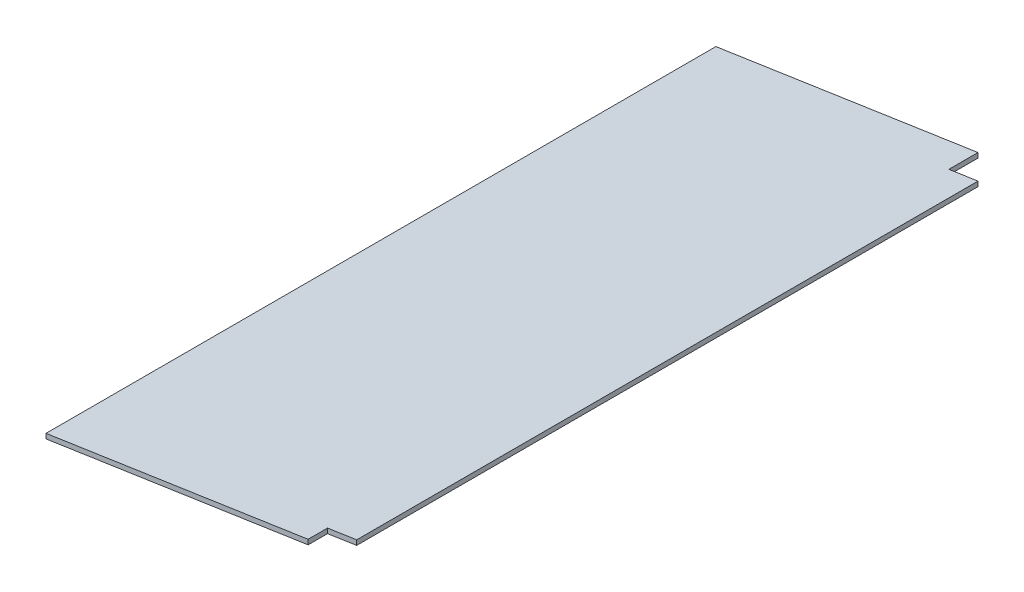
SolidWorks part; units mm, degrees
ref_plane "Front Plane" through (0, 0, 0) normal (0, 0, 1) x (1, 0, 0)
ref_plane "Top Plane" through (0, 0, 0) normal (0, 1, 0) x (1, 0, 0)
ref_plane "Right Plane" through (0, 0, 0) normal (1, 0, 0) x (0, 0, -1)
sketch "Sketch1" plane through (0, 0, 0) normal (0, 0, 1) x (1, 0, 0)
  line L0 (0, 0) -> (0, 5)
  line L1 (0, 0) -> (300, 0)
  line L2 (300, 0) -> (300, 50)
  line L3 (300, 50) -> (0, 5)
  line L4 (0, 0) -> (300, 45)
  dimension "D1" = 5
  dimension "D2" = 5
  dimension "D3" = 300
  dimension "D4" = 50
extrude "Boss-Extrude1" add sketch "Sketch1" along normal blind 690 contours L0 L4 L2 L3
sketch "Sketch3" plane through (0, 0, 0) normal (0, 1, 0) x (1, 0, 0)
  line L0 (270, -690) -> (300, -690)
  line L1 (300, -690) -> (300, -670)
  line L2 (300, -30) -> (300, 0)
  line L3 (300, -690) -> (270, -690)
  line L4 (300, -690) -> (300, -670)
  line L5 (300, -670) -> (270, -670)
  line L6 (270, -690) -> (270, -670)
  line L7 (300, 0) -> (270, 0)
  line L8 (300, 0) -> (300, -30)
  line L9 (300, -30) -> (270, -30)
  line L10 (270, 0) -> (270, -30)
  dimension "D2" = 30
  dimension "D3" = 20
  dimension "D4" = 30
  dimension "D5" = 30
  dimension "D6" = 690
extrude "Cut-Extrude2" cut sketch "Sketch3" along normal through all contours L6 L0 L1 L5 | L7 L10 L9 L2
